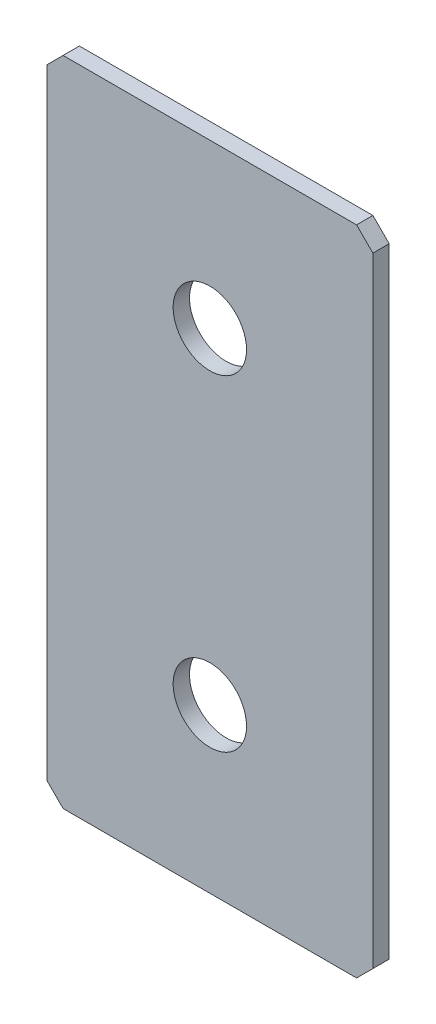
SolidWorks part; units mm, degrees
material "Простая углеродистая сталь"
ref_plane "Спереди(Плоскость XY)" through (0, 0, 0) normal (0, 0, 1) x (1, 0, 0)
ref_plane "Сверху(Плоскость XZ)" through (0, 0, 0) normal (0, 1, 0) x (1, 0, 0)
ref_plane "Справа(Плоскость ZY)" through (0, 0, 0) normal (1, 0, 0) x (0, 0, -1)
sketch "Эскиз1" plane through (0, 0, 0) normal (0, 0, 1) x (1, 0, 0)
  line L1 (-20, -40) -> (20, -40)
  line L2 (-20, -40) -> (-20, 40)
  line L3 (-20, 40) -> (20, 40)
  line L4 (20, -40) -> (20, 40)
  line L5 (-20, -40) -> (20, 40) construction
  line L6 (-20, 40) -> (20, -40) construction
  point P0 (0, 0)
  dimension "D1" = 40
  dimension "D2" = 80
extrude "Бобышка-Вытянуть1" add sketch "Эскиз1" along normal blind 2
chamfer "Фаска1" distance 2 angle 45 4 edges at (-20, -40, 1) (20, -40, 1) (-20, 40, 1) (20, 40, 1)
hole_wizard "Отверстие с зазором M81" positions "Эскиз2" profile "Эскиз3" hole size "M8" standard "DIN" end condition through all
sketch "Эскиз2" plane through (0, 0, 2) normal (0, 0, 1) x (1, 0, 0)
  line L12 (0, 40) -> (0, -40) construction
  line L13 (18, 40) -> (-18, 40) construction
  line L14 (-18, -40) -> (18, -40) construction
  point P206 (0, 20)
  point P208 (0, -20)
  dimension "D2" = 40
  dimension "D4" = 20
sketch "Эскиз3" plane through (0, -20, 2) normal (1, 0, 0) x (0, -1, 0)
  line L0 (0, 0) -> (0, 2)
  line L1 (0, 2) -> (4.5, 2)
  line L2 (4.5, 2) -> (4.5, 0)
  line L5 (4.5, 0) -> (0, 0)
  line L11 (0, -6.35) -> (0, 107.95) construction
  dimension "Диаметр сквозного отверстия" = 9
  dimension "Глубина сквозного отверстия" = 2
